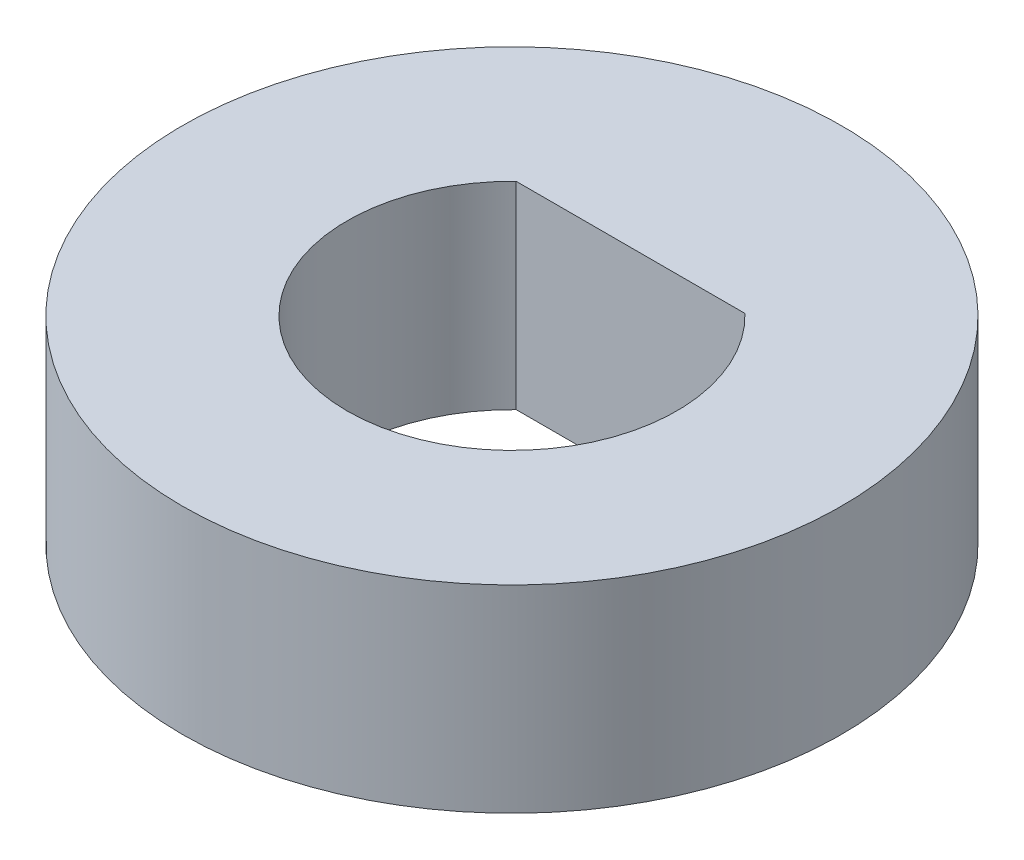
SolidWorks part; units mm, degrees
material "POM 乙缩醛共聚物"
ref_plane "前视基准面" through (0, 0, 0) normal (0, 0, 1) x (1, 0, 0)
ref_plane "上视基准面" through (0, 0, 0) normal (0, 1, 0) x (1, 0, 0)
ref_plane "右视基准面" through (0, 0, 0) normal (1, 0, 0) x (0, 0, -1)
sketch "草图1" plane through (0, 0, 0) normal (0, 1, 0) x (1, 0, 0)
  line L0 (-3.4699, 3.6) -> (3.4699, 3.6)
  arc A0 (-3.4699, 3.6) -> (3.4699, 3.6) centre (0, 0) ccw
  circle A1 centre (0, 0) radius 10
  dimension "D1" = 10
  dimension "D2" = 20
  dimension "D3" = 3.6
extrude "凸台-拉伸1" add sketch "草图1" along normal blind 6
